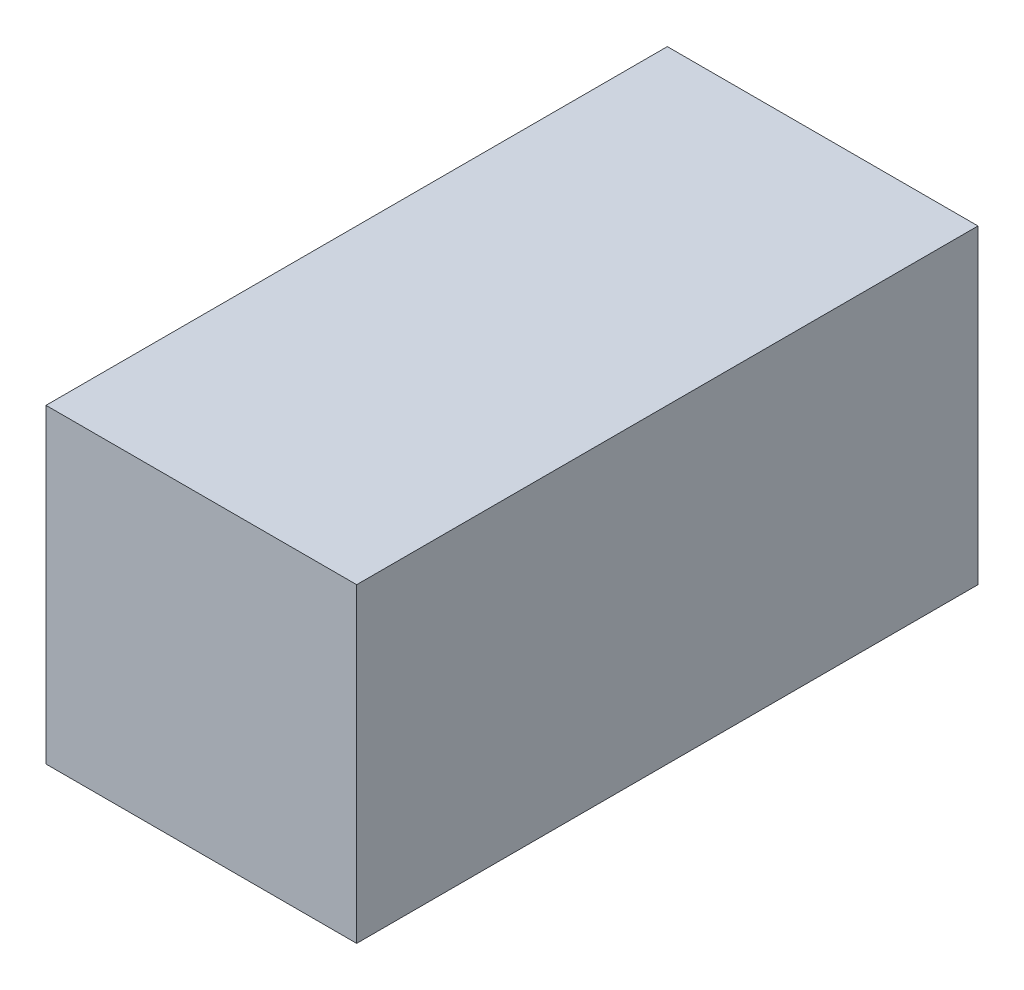
SolidWorks part; units mm, degrees
ref_plane "Front Plane" through (0, 0, 0) normal (0, 0, 1) x (1, 0, 0)
ref_plane "Top Plane" through (0, 0, 0) normal (0, 1, 0) x (1, 0, 0)
ref_plane "Right Plane" through (0, 0, 0) normal (1, 0, 0) x (0, 0, -1)
sketch "Sketch1" plane through (0, 0, 0) normal (0, 0, 1) x (1, 0, 0)
  line L1 (0, 0) -> (20, 0)
  line L2 (0, 0) -> (0, 20)
  line L3 (0, 20) -> (20, 20)
  line L4 (20, 0) -> (20, 20)
  dimension "D1" = 20
  dimension "D2" = 20
extrude "Boss-Extrude1" add sketch "Sketch1" along normal blind 40
